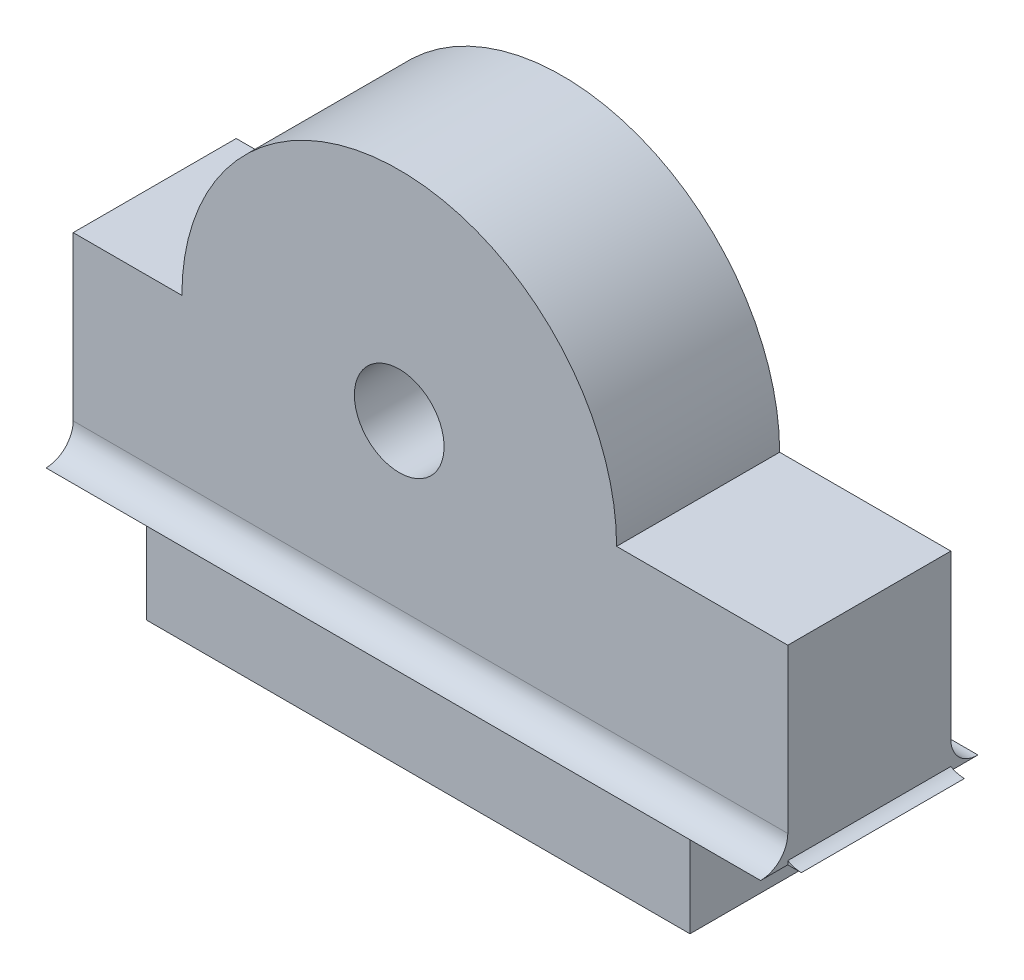
SolidWorks part; units mm, degrees
ref_plane "Front Plane" through (0, 0, 0) normal (0, 0, 1) x (1, 0, 0)
ref_plane "Top Plane" through (0, 0, 0) normal (0, 1, 0) x (1, 0, 0)
ref_plane "Right Plane" through (0, 0, 0) normal (1, 0, 0) x (0, 0, -1)
sketch "Sketch1" plane through (0, 0, 0) normal (0, 0, 1) x (1, 0, 0)
  line L0 (0, 0) -> (20, 0)
  line L1 (0, 0) -> (0, 4)
  line L2 (20, 0) -> (20, 4)
  line L3 (0, 4) -> (-2.7, 4)
  line L4 (23.6, 11) -> (23.6, 4)
  line L5 (-2.7, 4) -> (-2.7, 11)
  line L6 (-2.7, 11) -> (1.3, 11)
  line L7 (17.3, 11) -> (23.6, 11)
  line L8 (23.6, 4) -> (20, 4)
  line L9 (1.3, 11) -> (9.3, 11) construction
  line L10 (12.9373, 11) -> (9.3, 11) construction
  arc A0 (17.3, 11) -> (1.3, 11) centre (9.3, 11) ccw
  circle A1 centre (9.3, 11) radius 2.9
  point P19 (10, 0)
  point P22 (9.3, 11)
  dimension "D1" = 7
  dimension "D5" = 9.3
  dimension "D6" = 20
  dimension "D2" = 8
  dimension "D4" = 5.8
  dimension "D3" = 2.7
  dimension "D7" = 23.6
  dimension "D9" = 4
extrude "Boss-Extrude1" add sketch "Sketch1" along normal blind 6
sketch "Sketch2" plane through (-2.7, 0, 0) normal (-1, 0, 0) x (0, 0, 1)
  line L0 (3, 0) -> (3, 7) construction
  line L1 (6, 4) -> (6, 5)
  line L2 (6, 4) -> (7, 4)
  line L3 (0, 4) -> (-1, 4)
  line L4 (0, 4) -> (0, 5)
  arc A0 (6, 5) -> (7, 4) centre (7, 5) ccw
  arc A1 (0, 5) -> (-1, 4) centre (-1, 5) cw
  dimension "D1" = 1
  dimension "D2" = 1
  dimension "D3" = 6
  dimension "D4" = 3
  dimension "D5" = 4
extrude "Boss-Extrude2" add sketch "Sketch2" against normal up to surface (26.3 mm away) up to face at (23.6, 7.5, 3)
sketch "Sketch4" plane through (0, 0, 6) normal (0, 0, 1) x (1, 0, 0)
  line L0 (10.8, 0) -> (10.8, 7) construction
  line L1 (23.1, 4) -> (23.1, 5)
  line L2 (23.1, 4) -> (24.1, 4)
  line L3 (-1.5, 4) -> (-2.5, 4)
  line L4 (-1.5, 4) -> (-1.5, 5)
  arc A0 (23.1, 5) -> (24.1, 4) centre (24.1, 5) ccw
  arc A1 (-1.5, 5) -> (-2.5, 4) centre (-2.5, 5) cw
  dimension "D1" = 1
  dimension "D2" = 1
  dimension "D3" = 10.8
  dimension "D4" = 12.3
  dimension "D5" = 4
extrude "Boss-Extrude3" add sketch "Sketch4" against normal up to surface (6 mm away) up to face at (12.2, 11, 0)
sketch "Sketch5" plane through (0, 0, 6) normal (0, 0, -1) x (-1, 0, 0)
  line L0 (-9.3, 13.9) -> (-9.3, 8.1) construction
  circle A0 centre (-9.3, 11) radius 2.9 construction
  circle A1 centre (-9.3, 11) radius 1.65
  circle A2 centre (-9.3, 11) radius 2.9
  dimension "D1" = 3.3
  dimension "D2" = 5.8
extrude "Boss-Extrude4" add sketch "Sketch5" along normal blind 3
equation "\"D4@Sketch1\"= 5.5 + \"tol1@parametersSketch@prostheticParameters.SLDPRT\""
equation "\"D1@Sketch5\"= 3 + \"tol1@parametersSketch@prostheticParameters.SLDPRT\""
equation "\"D2@Sketch5\"= 5.5 + \"tol1@parametersSketch@prostheticParameters.SLDPRT\""
